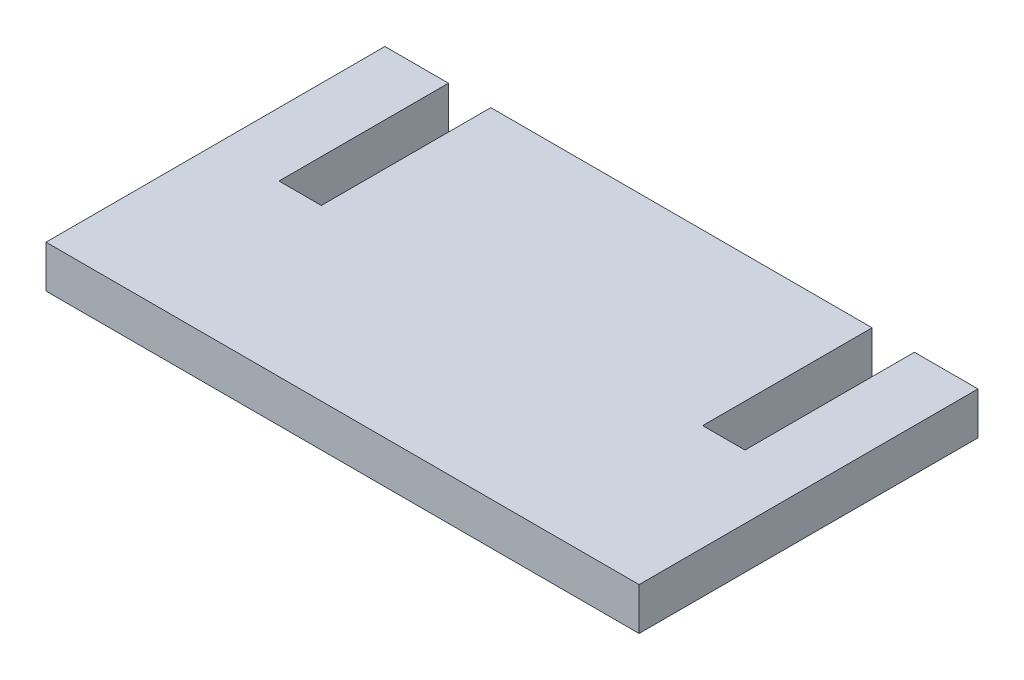
SolidWorks part; units mm, degrees
ref_plane "Front Plane" through (0, 0, 0) normal (0, 0, 1) x (1, 0, 0)
ref_plane "Top Plane" through (0, 0, 0) normal (0, 1, 0) x (1, 0, 0)
ref_plane "Right Plane" through (0, 0, 0) normal (1, 0, 0) x (0, 0, -1)
sketch "Sketch1" plane through (0, 0, 0) normal (0, 1, 0) x (1, 0, 0)
  line L1 (0, 0) -> (35.56, 0)
  line L2 (0, 0) -> (0, -20.32)
  line L3 (0, -20.32) -> (35.56, -20.32)
  line L4 (35.56, 0) -> (35.56, -20.32)
  dimension "D1" = 20.32
  dimension "D2" = 35.56
extrude "Boss-Extrude1" add sketch "Sketch1" along normal blind 2.54
sketch "Sketch2" plane through (0, 2.54, 0) normal (0, 1, 0) x (1, 0, 0)
  line L0 (35.56, 0) -> (0, 0) construction
  line L1 (3.81, 0) -> (6.35, 0)
  line L2 (3.81, 0) -> (3.81, -10.16)
  line L3 (3.81, -10.16) -> (6.35, -10.16)
  line L4 (6.35, 0) -> (6.35, -10.16)
  line L5 (0, 0) -> (0, -20.32) construction
  line L6 (29.21, 0) -> (31.75, 0)
  line L7 (29.21, 0) -> (29.21, -10.16)
  line L8 (29.21, -10.16) -> (31.75, -10.16)
  line L9 (31.75, 0) -> (31.75, -10.16)
  line L10 (35.56, -20.32) -> (35.56, 0) construction
  dimension "D1" = 3.81
  dimension "D2" = 2.54
  dimension "D3" = 3.81
  dimension "D4" = 2.54
  dimension "D5" = 10.16
  dimension "D6" = 10.16
extrude "Cut-Extrude1" cut sketch "Sketch2" against normal through all
